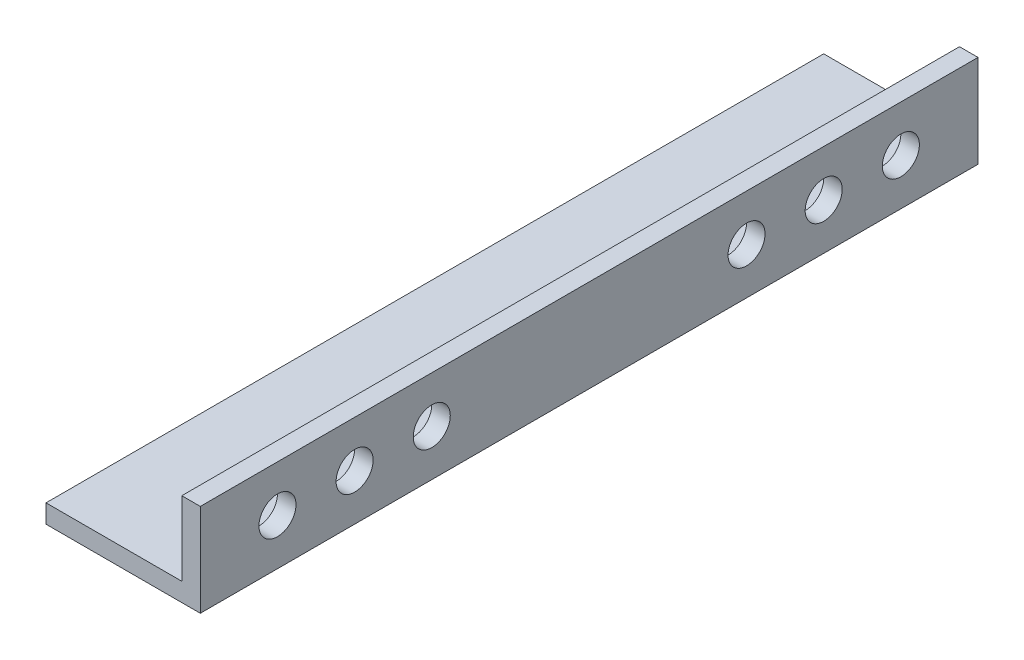
SolidWorks part; units mm, degrees
ref_plane "Alzado" through (0, 0, 0) normal (0, 0, 1) x (1, 0, 0)
ref_plane "Planta" through (0, 0, 0) normal (0, 1, 0) x (1, 0, 0)
ref_plane "Vista lateral" through (0, 0, 0) normal (1, 0, 0) x (0, 0, -1)
sketch "Croquis1" plane through (0, 0, 0) normal (0, 0, 1) x (1, 0, 0)
  line L0 (0, 0) -> (3, 0)
  line L1 (3, 0) -> (3, -15)
  line L2 (3, -15) -> (-22, -15)
  line L3 (-22, -15) -> (-22, -12)
  line L4 (-22, -12) -> (0, -12)
  line L5 (0, -12) -> (0, 0)
  dimension "D1" = 3
  dimension "D2" = 3
  dimension "D3" = 15
  dimension "D4" = 25
extrude "Saliente-Extruir1" add sketch "Croquis1" along normal blind 126
sketch "Croquis2" plane through (3, 0, 0) normal (1, 0, 0) x (0, 0, -1)
  line L0 (-126, -7.5) -> (-113.5, -7.5) construction
  line L1 (-126, -15) -> (-126, 0) construction
  line L2 (-63, -15) -> (-63, 0) construction
  line L3 (-126, -15) -> (0, -15) construction
  line L4 (-126, 0) -> (0, 0) construction
  circle A0 centre (-113.5, -7.5) radius 3
  circle A1 centre (-101, -7.5) radius 3
  circle A2 centre (-88.5, -7.5) radius 3
  circle A3 centre (-12.5, -7.5) radius 3
  circle A4 centre (-25, -7.5) radius 3
  circle A5 centre (-37.5, -7.5) radius 3
  dimension "D2" = 6
  dimension "D3" = 6
  dimension "D1" = 12.5
  dimension "D4" = 12.5
  dimension "D5" = 12.5
extrude "Cortar-Extruir3" cut sketch "Croquis2" against normal mid plane 126
